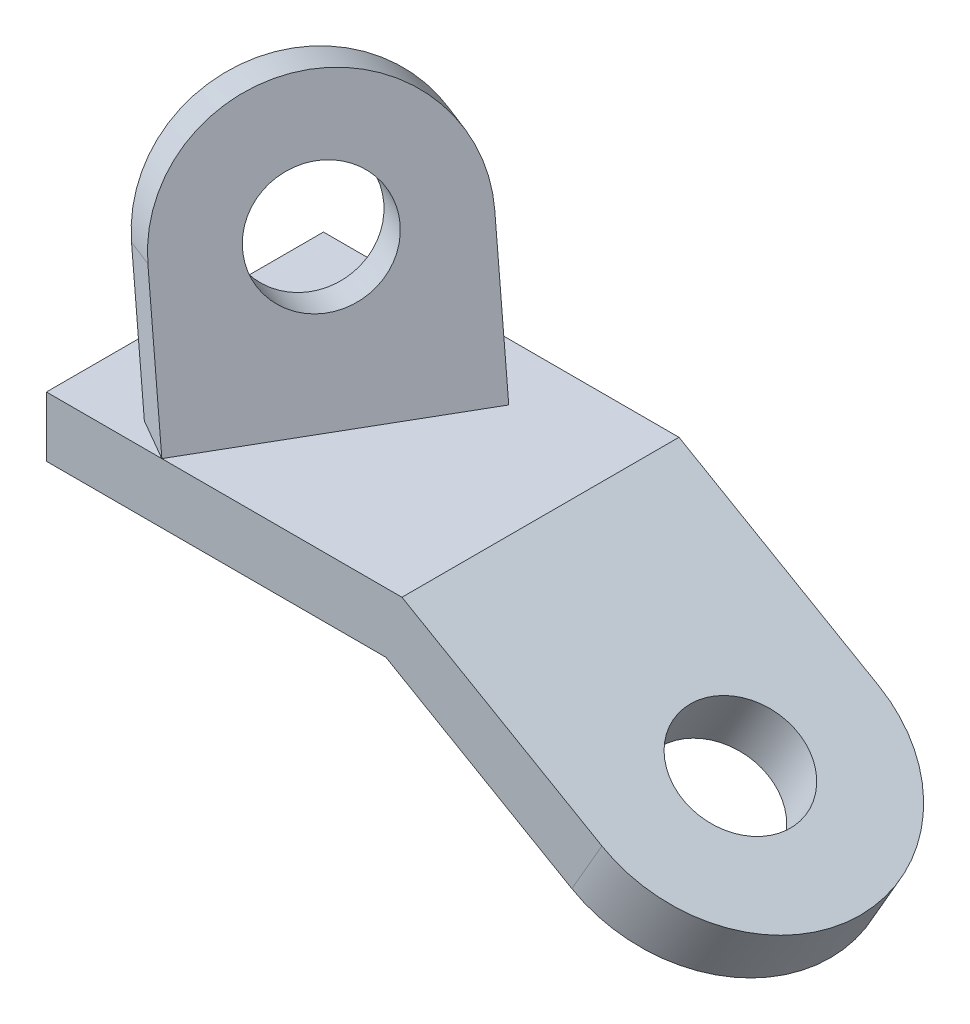
SolidWorks part; units mm, degrees
ref_plane "Front Plane" through (0, 0, 0) normal (0, 0, 1) x (1, 0, 0)
ref_plane "Top Plane" through (0, 0, 0) normal (0, 1, 0) x (1, 0, 0)
ref_plane "Right Plane" through (0, 0, 0) normal (1, 0, 0) x (0, 0, -1)
sketch "Sketch1" plane through (0, 0, 0) normal (0, 0, 1) x (1, 0, 0)
  line L0 (0, 0) -> (0, 13)
  line L1 (0, 13) -> (77, 13)
  line L2 (77, 13) -> (146.282, -27)
  line L3 (146.282, -27) -> (139.782, -38.2583)
  line L4 (139.782, -38.2583) -> (73.5167, 0)
  line L5 (73.5167, 0) -> (0, 0)
  point P3 (62.4, 13)
  point P8 (62.1524, 13)
  dimension "D1" = 13
  dimension "D2" = 13
  dimension "D3" = 150
  dimension "D4" = 80
  dimension "D5" = 77
extrude "Boss-Extrude1" add sketch "Sketch1" against normal blind 60
sketch "Sketch2" plane through (24.8792, 43.092, 0) normal (0.5, 0.866, 0) x (0.866, -0.5, 0)
  line L0 (140.184, 60) -> (140.184, 0) construction
  line L1 (110.184, 30) -> (110.184, 61.0479)
  line L2 (110.184, 61.0479) -> (110.184, 0)
  line L3 (110.184, 60) -> (140.184, 60)
  line L4 (140.184, 60) -> (60.184, 60) construction
  line L5 (140.184, 60) -> (140.184, 0)
  line L6 (140.184, 0) -> (110.184, 0)
  arc A0 (110.184, 0) -> (110.184, 60) centre (110.184, 30) ccw
  line M2 (60.184, 0) -> (140.184, 0)
  line M3 (140.184, 0) -> (140.184, 60)
  line M4 (140.184, 60) -> (60.184, 60)
  dimension "D2" = 60
  dimension "D1" = 30
extrude "Cut-Extrude1" cut sketch "Sketch2" against normal blind 60 contours A0 L5 M4 | A0 M2 M3
sketch "Sketch3" plane through (24.8792, 43.092, 0) normal (0.5, 0.866, 0) x (0.866, -0.5, 0)
  circle A0 centre (110.184, 30) radius 12.5
  dimension "D1" = 25
extrude "Cut-Extrude2" cut sketch "Sketch3" against normal blind 60
sketch "Sketch4" plane through (0, 13, 0) normal (0, 1, 0) x (1, 0, 0)
  line L0 (0, 0) -> (25, 0) construction
  line L1 (77, 0) -> (0, 0) construction
  line L2 (25, 0) -> (51.8895, 46.5739) construction
  dimension "D1" = 25
  dimension "D2" = 120
ref_plane "Plane1" through (20.3086, 6.2835, 11.7252) normal (0.8365, 0.2588, 0.483) x (0.5, 0, -0.866)
sketch "Sketch5" plane through (20.3086, 6.2835, 11.7252) normal (0.8365, 0.2588, 0.483) x (0.5, 0, -0.866)
  line L0 (12.5, 6.9534) -> (67.5, 6.9534)
  line L1 (67.5, 6.9534) -> (67.5, 38.9534)
  line L3 (12.5, 38.9534) -> (12.5, 6.9534)
  arc A0 (67.5, 38.9534) -> (12.5, 38.9534) centre (40, 38.9534) ccw
  point P6 (0, 0)
  point P7 (40, 6.9534)
  dimension "D3" = 27.5
  dimension "D1" = 55
  dimension "D2" = 32
extrude "Boss-Extrude2" add sketch "Sketch5" against normal blind 10
sketch "Sketch6" plane through (20.3086, 6.2835, 11.7252) normal (0.8365, 0.2588, 0.483) x (0.4614, 0.1428, -0.8756)
  circle A0 centre (45.3176, 32.6142) radius 12.5
  dimension "D1" = 25
extrude "Cut-Extrude3" cut sketch "Sketch6" against normal blind 59
